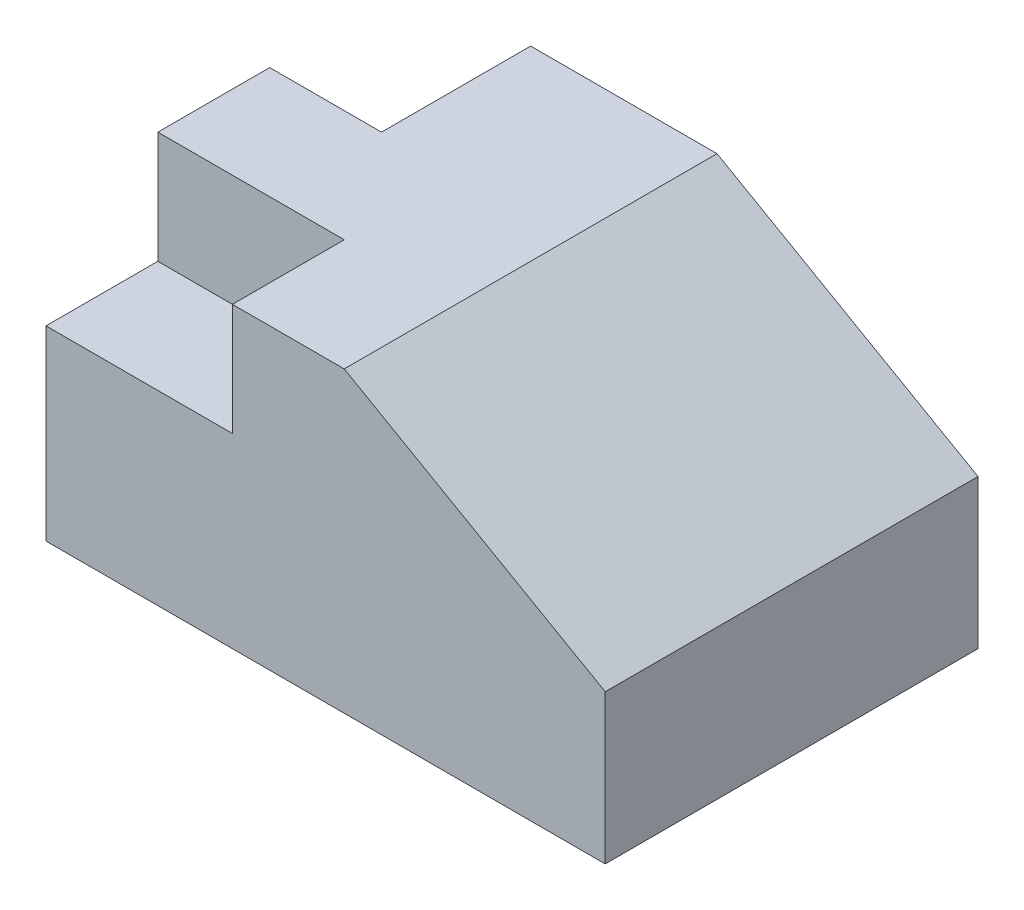
SolidWorks part; units mm, degrees
ref_plane "Front Plane" through (0, 0, 0) normal (0, 0, 1) x (1, 0, 0)
ref_plane "Top Plane" through (0, 0, 0) normal (0, 1, 0) x (1, 0, 0)
ref_plane "Right Plane" through (0, 0, 0) normal (1, 0, 0) x (0, 0, -1)
sketch "Sketch1" plane through (0, 0, 0) normal (0, 0, 1) x (1, 0, 0)
  line L0 (-53.5433, -47.4541) -> (96.4567, -47.4541)
  line L1 (96.4567, -47.4541) -> (96.4567, -7.4541)
  line L2 (96.4567, -7.4541) -> (26.4567, 32.5459)
  line L3 (26.4567, 32.5459) -> (-53.5433, 32.5459)
  line L4 (-53.5433, 32.5459) -> (-53.5433, -47.4541)
  dimension "D1" = 80
  dimension "D2" = 40
  dimension "D3" = 150
  dimension "D4" = 80
extrude "Boss-Extrude1" add sketch "Sketch1" against normal blind 100
sketch "Sketch2" plane through (0, 0, 0) normal (0, 0, 1) x (1, 0, 0)
  line L1 (-3.5433, 2.5459) -> (-53.5433, 2.5459)
  line L2 (-3.5433, 2.5459) -> (-3.5433, 32.5459)
  line L3 (-3.5433, 32.5459) -> (-53.5433, 32.5459)
  line L4 (-53.5433, 2.5459) -> (-53.5433, 32.5459)
  dimension "D1" = 50
  dimension "D2" = 30
extrude "Cut-Extrude1" cut sketch "Sketch2" against normal blind 30
sketch "Sketch3" plane through (0, 32.5459, 0) normal (0, 1, 0) x (1, 0, 0)
  line L1 (-23.5433, 60) -> (-53.5433, 60)
  line L2 (-23.5433, 60) -> (-23.5433, 100)
  line L3 (-23.5433, 100) -> (-53.5433, 100)
  line L4 (-53.5433, 60) -> (-53.5433, 100)
  dimension "D1" = 40
  dimension "D2" = 30
extrude "Cut-Extrude2" cut sketch "Sketch3" against normal blind 80
